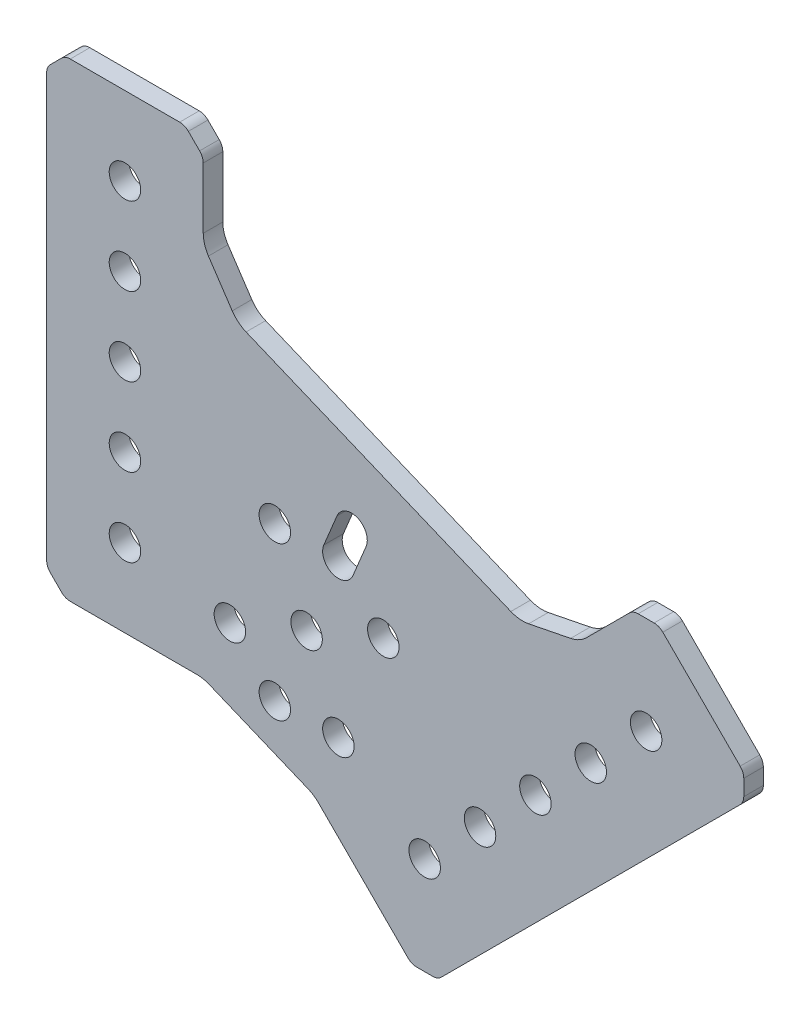
SolidWorks part; units mm, degrees
material "5052-H32"
ref_plane "Front Plane" through (0, 0, 0) normal (0, 0, 1) x (1, 0, 0)
ref_plane "Top Plane" through (0, 0, 0) normal (0, 1, 0) x (1, 0, 0)
ref_plane "Right Plane" through (0, 0, 0) normal (1, 0, 0) x (0, 0, -1)
ref_plane "Plane1" through (0, 0, 0) normal (0, 0, -1) x (-1, 0, 0)
sketch "Sketch1" plane through (0, 0, 0) normal (0, 0, -1) x (-1, 0, 0)
  line L0 (-49.6787, 26.5434) -> (-51.8139, 31.6983)
  line L1 (-47.0971, 33.652) -> (-44.9619, 28.4972)
  line L2 (-2.4142, 0.5858) -> (-0.5858, 2.4142)
  line L3 (0, 3.8284) -> (0, 72.3716)
  line L4 (-0.5858, 73.7858) -> (-2.4142, 75.6142)
  line L5 (-3.8284, 76.2) -> (-21.5716, 76.2)
  line L6 (-22.9858, 75.6142) -> (-24.8142, 73.7858)
  line L7 (-25.4, 72.3716) -> (-25.4, 62.5023)
  line L8 (-26.2427, 59.7244) -> (-30.1006, 53.9505)
  line L9 (-32.3446, 52.109) -> (-75.2966, 34.3177)
  line L10 (-78.1855, 34.0331) -> (-84.9962, 35.3879)
  line L11 (-87.5563, 36.7563) -> (-94.5349, 43.7349)
  line L12 (-95.9492, 44.3207) -> (-98.5349, 44.3207)
  line L13 (-99.9492, 43.7349) -> (-112.4955, 31.1886)
  line L14 (-113.0812, 29.7744) -> (-113.0812, 27.1886)
  line L15 (-112.4955, 25.7744) -> (-64.0281, -22.6929)
  line L16 (-62.6139, -23.2787) -> (-60.0281, -23.2787)
  line L17 (-58.6139, -22.6929) -> (-44.0638, -8.1427)
  line L18 (-42.4417, -7.0589) -> (-26.3189, -0.3806)
  line L19 (-24.4054, 0) -> (-3.8284, 0)
  circle A0 centre (-29.7204, 9.9204) radius 2.5527
  circle A1 centre (-47.3203, 2.6303) radius 2.5527
  circle A2 centre (-12.7, 12.7) radius 2.5527
  circle A3 centre (-12.7, 38.1) radius 2.5527
  circle A4 centre (-12.7, 63.5) radius 2.5527
  circle A5 centre (-12.7, 25.4) radius 2.5527
  circle A6 centre (-12.7, 50.8) radius 2.5527
  circle A7 centre (-70.3013, 1.5408) radius 2.5527
  circle A8 centre (-88.2618, 19.5013) radius 2.5527
  circle A9 centre (-97.242, 28.4815) radius 2.5527
  circle A10 centre (-79.2815, 10.521) radius 2.5527
  circle A11 centre (-61.321, -7.4395) radius 2.5527
  circle A12 centre (-37.0105, 27.5203) radius 2.5527
  circle A13 centre (-54.6104, 20.2302) radius 2.5527
  circle A14 centre (-42.1654, 15.0753) radius 2.5527
  circle A15 centre (-37.0105, 2.6303) radius 2.5527
  arc A16 (-51.8139, 31.6983) -> (-47.0971, 33.652) centre (-49.4555, 32.6752) cw
  arc A17 (-44.9619, 28.4972) -> (-49.6787, 26.5434) centre (-47.3203, 27.5203) cw
  arc A18 (-0.5858, 2.4142) -> (0, 3.8284) centre (-2, 3.8284) ccw
  arc A19 (0, 72.3716) -> (-0.5858, 73.7858) centre (-2, 72.3716) ccw
  arc A20 (-2.4142, 75.6142) -> (-3.8284, 76.2) centre (-3.8284, 74.2) ccw
  arc A21 (-21.5716, 76.2) -> (-22.9858, 75.6142) centre (-21.5716, 74.2) ccw
  arc A22 (-24.8142, 73.7858) -> (-25.4, 72.3716) centre (-23.4, 72.3716) ccw
  arc A23 (-25.4, 62.5023) -> (-26.2427, 59.7244) centre (-30.4, 62.5023) cw
  arc A24 (-30.1006, 53.9505) -> (-32.3446, 52.109) centre (-34.258, 56.7284) cw
  arc A25 (-75.2966, 34.3177) -> (-78.1855, 34.0331) centre (-77.21, 38.9371) cw
  arc A26 (-84.9962, 35.3879) -> (-87.5563, 36.7563) centre (-84.0207, 40.2918) cw
  arc A27 (-94.5349, 43.7349) -> (-95.9492, 44.3207) centre (-95.9492, 42.3207) ccw
  arc A28 (-98.5349, 44.3207) -> (-99.9492, 43.7349) centre (-98.5349, 42.3207) ccw
  arc A29 (-112.4955, 31.1886) -> (-113.0812, 29.7744) centre (-111.0812, 29.7744) ccw
  arc A30 (-113.0812, 27.1886) -> (-112.4955, 25.7744) centre (-111.0812, 27.1886) ccw
  arc A31 (-64.0281, -22.6929) -> (-62.6139, -23.2787) centre (-62.6139, -21.2787) ccw
  arc A32 (-60.0281, -23.2787) -> (-58.6139, -22.6929) centre (-60.0281, -21.2787) ccw
  arc A33 (-44.0638, -8.1427) -> (-42.4417, -7.0589) centre (-40.5282, -11.6783) cw
  arc A34 (-26.3189, -0.3806) -> (-24.4054, 0) centre (-24.4054, -5) cw
  arc A35 (-3.8284, 0) -> (-2.4142, 0.5858) centre (-3.8284, 2) ccw
extrude "Boss-Extrude1" add sketch "Sketch1" against normal blind 3.175
